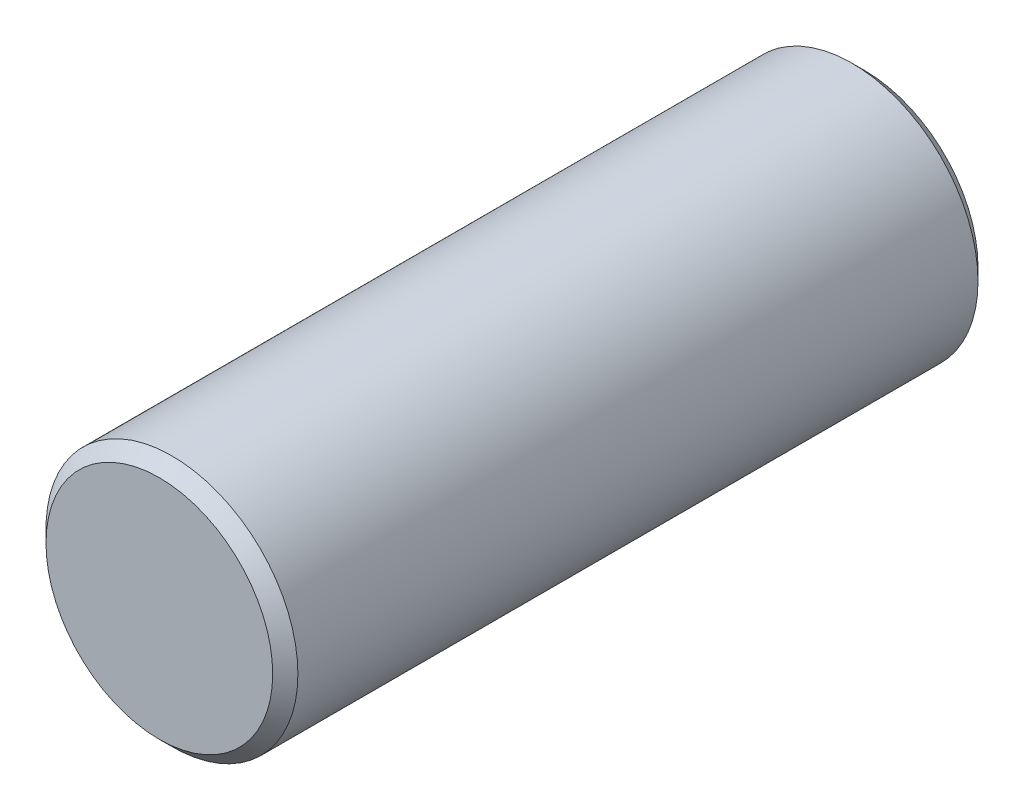
SolidWorks part; units mm, degrees
material "AISI 1020"
ref_plane "Front Plane" through (0, 0, 0) normal (0, 0, 1) x (1, 0, 0)
ref_plane "Top Plane" through (0, 0, 0) normal (0, 1, 0) x (1, 0, 0)
ref_plane "Right Plane" through (0, 0, 0) normal (1, 0, 0) x (0, 0, -1)
sketch "Sketch1" plane through (0, 0, 0) normal (0, 0, 1) x (1, 0, 0)
  circle A0 centre (0, 0) radius 5
extrude "Boss-Extrude1" add sketch "Sketch1" along normal blind 28
chamfer "Chamfer1" distance 0.5 angle 45 2 edges at (5, 0, 0) (5, 0, 28)
